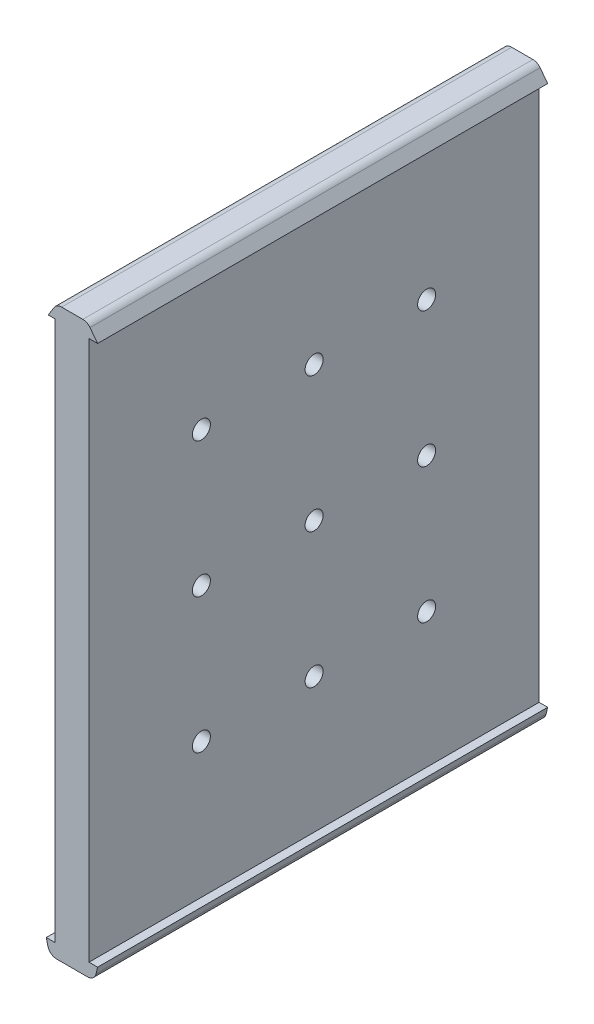
SolidWorks part; units mm, degrees
ref_plane "Plano frontal" through (0, 0, 0) normal (0, 0, 1) x (1, 0, 0)
ref_plane "Plano superior" through (0, 0, 0) normal (0, 1, 0) x (1, 0, 0)
ref_plane "Plano direito" through (0, 0, 0) normal (1, 0, 0) x (0, 0, -1)
sketch "Esboço1" plane through (0, 0, 0) normal (0, 0, 1) x (1, 0, 0)
  line L0 (0, 0) -> (0, 14.1176) construction
  line L1 (-3.8, -98.1786) -> (-5.7, -98.1786)
  line L2 (0, -101.1786) -> (0, -98.1786) construction
  line L3 (0, -98.1786) -> (-3.8, -98.1786) construction
  line L4 (-3.4129, -101.1786) -> (3.4129, -101.1786)
  line L5 (3.8, -98.1786) -> (0, -98.1786) construction
  line L6 (5.7, -98.1786) -> (5.7, -30.5351) construction
  line L7 (-5.3606, -99.6331) -> (-5.7, -98.1786)
  line L8 (5.7, -98.1786) -> (5.3606, -99.6331)
  line L9 (5.7, -30.5351) -> (5.7, 21.8214) construction
  line L10 (5.7, 21.8214) -> (3.4129, 21.8214) construction
  line L11 (3.8, -98.1786) -> (3.8, 21.8214)
  line L12 (3.8, 21.8214) -> (3.4129, 21.8214)
  line L13 (-3.8, -98.1786) -> (-3.8, 21.8214)
  line L14 (3.8, -98.1786) -> (5.7, -98.1786)
  line L15 (-5.2668, 21.8214) -> (-5.2668, 17.6583) construction
  line L16 (3.4129, -101.1786) -> (3.4129, 21.8214) construction
  line L17 (-3.4129, -101.1786) -> (-3.4129, 24.8214) construction
  line L18 (5.7, 21.8214) -> (3.4129, 21.8214)
  line L19 (3.4129, 21.8214) -> (3.4129, 24.8214) construction
  line L20 (5.7, 21.8214) -> (4.0133, 24.0339)
  line L21 (2.4227, 24.8214) -> (-2.2978, 24.8214)
  line L22 (-3.9992, 23.8727) -> (-5.2668, 21.8214)
  line L23 (-3.4129, 21.8214) -> (-5.2668, 21.8214) construction
  line L24 (-3.4129, 21.8214) -> (-3.8, 21.8214)
  line L25 (-3.4129, 21.8214) -> (-5.2668, 21.8214)
  arc A0 (3.4129, -101.1786) -> (5.3606, -99.6331) centre (3.4129, -99.1786) ccw
  arc A1 (-5.3606, -99.6331) -> (-3.4129, -101.1786) centre (-3.4129, -99.1786) ccw
  arc A2 (-2.2978, 24.8214) -> (-3.9992, 23.8727) centre (-2.2978, 22.8214) ccw
  arc A3 (2.4227, 24.8214) -> (4.0133, 24.0339) centre (2.4227, 22.8214) cw
  point P15 (5, -101.1786)
  point P18 (-5, -101.1786)
  dimension "D9" = 2
  dimension "D11" = 2
  dimension "D1" = 5.7
  dimension "D2" = 5.7
  dimension "D3" = 11.4
  dimension "D4" = 5.7
  dimension "D5" = 5
  dimension "D6" = 7.6
  dimension "D7" = 3.8
  dimension "D8" = 120
  dimension "D10" = 3
  dimension "D12" = 3
extrude "Ressalto-extrusão1" add sketch "Esboço1" along normal blind 160
sketch "Esboço2" plane through (0, 0, 0) normal (0, 0, 1) x (1, 0, 0)
  line L1 (-3.8, 21.8214) -> (3.8, 21.8214)
  line L2 (-3.8, 21.8214) -> (-3.8, -98.1786)
  line L3 (-3.8, -98.1786) -> (3.8, -98.1786)
  line L4 (3.8, 21.8214) -> (3.8, -98.1786)
extrude "Corte-extrusão1" cut sketch "Esboço2" along normal blind 30
sketch3d "3DSketch2"
  line L1 (-3.8, 21.8214, 160) -> (3.8, 21.8214, 160)
  line L2 (-3.8, 21.8214, 160) -> (-3.8, -98.1786, 160)
  line L3 (-3.8, -98.1786, 160) -> (3.8, -98.1786, 160)
  line L4 (3.8, 21.8214, 160) -> (3.8, -98.1786, 160)
  dimension "D1" = 160
extrude "Corte-extrusão2" cut sketch "3DSketch2" along direction (0, 0, 1) on the side of the normal blind 30
sketch3d "3DSketch3"
  line L0 (3.8, 21.8214, 130) -> (3.8, 21.8214, 80) construction
  line L1 (3.8, 21.8214, 130) -> (3.8, 21.8214, 30) construction
  line L2 (3.8, 21.8214, 80) -> (3.8, -98.1786, 80) construction
  line L3 (3.8, -98.1786, 130) -> (3.8, -98.1786, 30) construction
  line L4 (3.8, -98.1786, 80) -> (3.8, -98.1786, 130) construction
  line L5 (3.8, -98.1786, 130) -> (3.8, -38.1786, 130) construction
  line L6 (3.8, -98.1786, 130) -> (3.8, 21.8214, 130) construction
  line L7 (3.8, -38.1786, 130) -> (3.8, -38.1786, 30) construction
  line L8 (3.8, -98.1786, 30) -> (3.8, 21.8214, 30) construction
  line L9 (3.8, 21.8214, 130) -> (3.8, -98.1786, 30) construction
  line L10 (3.8, -98.1786, 30) -> (3.8, -98.1786, 130) construction
  line L11 (3.8, -98.1786, 130) -> (3.8, 21.8214, 30) construction
  line L12 (3.8, 21.8214, 30) -> (3.8, -38.1786, 130) construction
  line L13 (3.8, -38.1786, 130) -> (3.8, 21.8214, 130) construction
  line L14 (3.8, 21.8214, 130) -> (3.8, -38.1786, 30) construction
  line L15 (3.8, -38.1786, 30) -> (3.8, -8.1786, 30) construction
  line L16 (3.8, -8.1786, 30) -> (3.8, -8.1786, 130) construction
  line L17 (3.8, -38.1786, 130) -> (3.8, -98.1786, 30) construction
  line L18 (3.8, -98.1786, 30) -> (3.8, -98.1786, 130) construction
  line L19 (3.8, -98.1786, 130) -> (3.8, -38.1786, 30) construction
  line L20 (3.8, -68.1786, 80) -> (3.8, -68.1786, 30) construction
  line L21 (3.8, -68.1786, 30) -> (3.8, -68.1786, 130) construction
  line L22 (3.8, 21.8214, 105) -> (3.8, -98.1786, 80) construction
  line L23 (3.8, -98.1786, 80) -> (3.8, -98.1786, 105) construction
  line L24 (3.8, -98.1786, 105) -> (3.8, 21.8214, 80) construction
  line L25 (3.8, 21.8214, 80) -> (3.8, -98.1786, 55) construction
  line L26 (3.8, -98.1786, 55) -> (3.8, 21.8214, 55) construction
  line L27 (3.8, 21.8214, 55) -> (3.8, -98.1786, 80) construction
  line L28 (3.8, -98.1786, 80) -> (3.8, -38.1786, 67.5) construction
  line L29 (3.8, -38.1786, 67.5) -> (3.8, -98.1786, 67.5) construction
  line L30 (3.8, -98.1786, 67.5) -> (3.8, 21.8214, 67.5) construction
  line L31 (3.8, -38.1786, 92.5213) -> (3.8, 21.8214, 92.5213) construction
  line L32 (3.8, 21.8214, 92.5213) -> (3.8, -98.1786, 92.5213) construction
  circle A0 centre (3.8, -38.1786, 80) radius 2
  circle A1 centre (3.8, -8.1786, 80) radius 2
  circle A2 centre (3.8, -68.1786, 80) radius 2
  circle A3 centre (3.8, -68.1786, 55) radius 2
  circle A4 centre (3.8, -38.1786, 55) radius 2
  circle A5 centre (3.8, -8.1786, 55) radius 2
  circle A6 centre (3.8, -68.1786, 105.0426) radius 2
  circle A7 centre (3.8, -38.1786, 105.0426) radius 2
  circle A8 centre (3.8, -8.1786, 105.0426) radius 2
  point P18 (5.8, -38.1786, 80)
  point P27 (5.8, -8.1786, 80)
  point P32 (5.8, -68.1786, 80)
  point P42 (5.8, -68.1786, 55)
  point P45 (5.8, -38.1786, 55)
  point P48 (5.8, -8.1786, 55)
  point P54 (5.8, -68.1786, 105.0426)
  point P57 (5.8, -38.1786, 105.0426)
  point P60 (5.8, -8.1786, 105.0426)
extrude "Corte-extrusão3" cut sketch "3DSketch3" along direction (-1, 0, 0) on the side against the normal blind 70
sketch "Esboço3" plane through (0, 0, 0) normal (1, 0, 0) x (0, 0, -1)
  line L0 (-130, 21.8214) -> (-130, 24.8214) construction
  line L1 (-160, 24.8214) -> (0, 24.8214) construction
  line L2 (-130, 24.8214) -> (-30, 21.8214) construction
  line L3 (-30, 21.8214) -> (-30, 24.8214) construction
  line L4 (-30, -98.1786) -> (-30, -101.1786) construction
  line L5 (-160, -101.1786) -> (0, -101.1786) construction
  line L6 (-30, -101.1786) -> (-130, -98.1786) construction
  line L7 (-130, -98.1786) -> (-130, -101.1786) construction
  line L9 (-30, 24.8214) -> (15.0153, 24.8214)
  line L10 (-30, 24.8214) -> (-30, -104.6572)
  line L11 (-30, -104.6572) -> (15.0153, -104.6572)
  line L12 (15.0153, 24.8214) -> (15.0153, -104.6572)
  line L13 (-130, 24.8214) -> (-167.1926, 24.8214)
  line L14 (-130, 24.8214) -> (-130, -104.6572)
  line L15 (-130, -104.6572) -> (-167.1926, -104.6572)
  line L16 (-167.1926, 24.8214) -> (-167.1926, -104.6572)
  circle A0 centre (-80, -8.1786) radius 2 construction
extrude "Corte-extrusão4" cut sketch "Esboço3" along normal blind 41 and the other way blind 22
